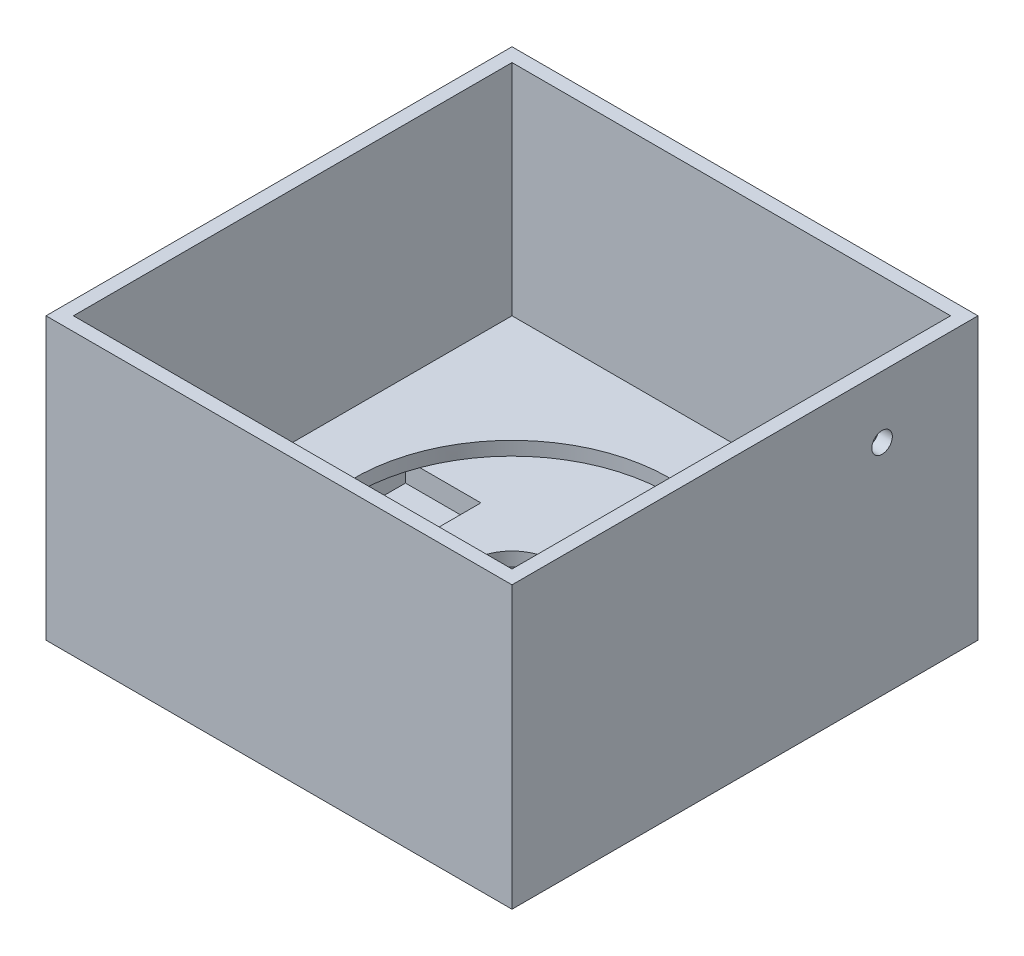
SolidWorks part; units mm, degrees
ref_plane "Front Plane" through (0, 0, 0) normal (0, 0, 1) x (1, 0, 0)
ref_plane "Top Plane" through (0, 0, 0) normal (0, 1, 0) x (1, 0, 0)
ref_plane "Right Plane" through (0, 0, 0) normal (1, 0, 0) x (0, 0, -1)
sketch "Sketch1" plane through (0, 0, 0) normal (0, 1, 0) x (1, 0, 0)
  line L1 (-34, -34) -> (34, -34)
  line L2 (-34, -34) -> (-34, 34)
  line L3 (-34, 34) -> (34, 34)
  line L4 (34, -34) -> (34, 34)
  line L5 (-34, -34) -> (34, 34) construction
  line L6 (-34, 34) -> (34, -34) construction
  point P0 (0, 0)
  dimension "D1" = 68
extrude "Boss-Extrude1" add sketch "Sketch1" along normal blind 41
sketch "Sketch2" plane through (0, 0, 0) normal (0, 1, 0) x (1, 0, 0)
  line L1 (-32, -32) -> (32, -32)
  line L2 (-32, -32) -> (-32, 32)
  line L3 (-32, 32) -> (32, 32)
  line L4 (32, -32) -> (32, 32)
  line L5 (-32, -32) -> (32, 32) construction
  line L6 (-32, 32) -> (32, -32) construction
  point P0 (0, 0)
  dimension "D1" = 64
extrude "Cut-Extrude1" cut sketch "Sketch2" against normal blind 32 from surface at 41 starting at face at (0, 41, 0)
sketch "Sketch3" plane through (0, 0, 0) normal (0, 1, 0) x (1, 0, 0)
  circle A0 centre (0, 0) radius 23
  dimension "D1" = 46
extrude "Cut-Extrude4" cut sketch "Sketch3" against normal blind 2 from surface at 9 starting at face at (0, 9, 0)
sketch "Sketch4" plane through (0, 7, 0) normal (0, 1, 0) x (1, 0, 0)
  line L1 (-12.6259, -7.9138) -> (-23.6259, -7.9138)
  line L2 (-12.6259, -7.9138) -> (-12.6259, 8.0862)
  line L3 (-12.6259, 8.0862) -> (-23.6259, 8.0862)
  line L4 (-23.6259, -7.9138) -> (-23.6259, 8.0862)
  circle A4 centre (-16.6259, 0.0862) radius 1.75
  point P7 (-23.7908, 1.3867)
  dimension "D1" = 11
  dimension "D2" = 4
sketch "Sketch5" plane through (0, 0, 0) normal (0, 1, 0) x (1, 0, 0)
  circle A0 centre (0, 0) radius 6.05
  dimension "D1" = 12.1
extrude "Cut-Extrude9" cut sketch "Sketch5" against normal through all from surface at 7 starting at face at (0, 7, 23)
sketch "Sketch6" plane through (0, 0, 0) normal (0, -1, 0) x (1, 0, 0)
  circle A0 centre (0, 0) radius 10.5
  dimension "D1" = 21
extrude "Cut-Extrude10" cut sketch "Sketch6" against normal blind 5 from surface at 0 starting at face at (0, 0, 6.05)
sketch "Sketch7" plane through (0, 0, 0) normal (0, -1, 0) x (-1, 0, 0)
  line L0 (-34, 34) -> (34, -34) construction
  line L1 (-34, -34) -> (34, 34) construction
  line L3 (-15, 15) -> (15, 15)
  line L4 (-15, 15) -> (-15, -15)
  line L5 (-15, -15) -> (15, -15)
  line L6 (15, 15) -> (15, -15)
  line L7 (-13, 13) -> (13, 13)
  line L8 (-13, 13) -> (-13, -13)
  line L9 (-13, -13) -> (13, -13)
  line L10 (13, 13) -> (13, -13)
  point P8 (0, 0)
  dimension "D1" = 30
  dimension "D2" = 26
extrude "Cut-Extrude11" cut sketch "Sketch7" against normal blind 2
sketch "Sketch8" plane through (32, 0, 0) normal (-1, 0, 0) x (0, 0, 1)
  line L0 (32, 9) -> (-32, 9) construction
  line L1 (-32, 9) -> (-32, 41) construction
  circle A0 centre (-20, 32) radius 1.5
  dimension "D1" = 3
  dimension "D2" = 23
  dimension "D3" = 12
extrude "Cut-Extrude12" cut sketch "Sketch8" against normal through all
extrude "Cut-Extrude13" cut sketch "Sketch4" against normal blind 3
